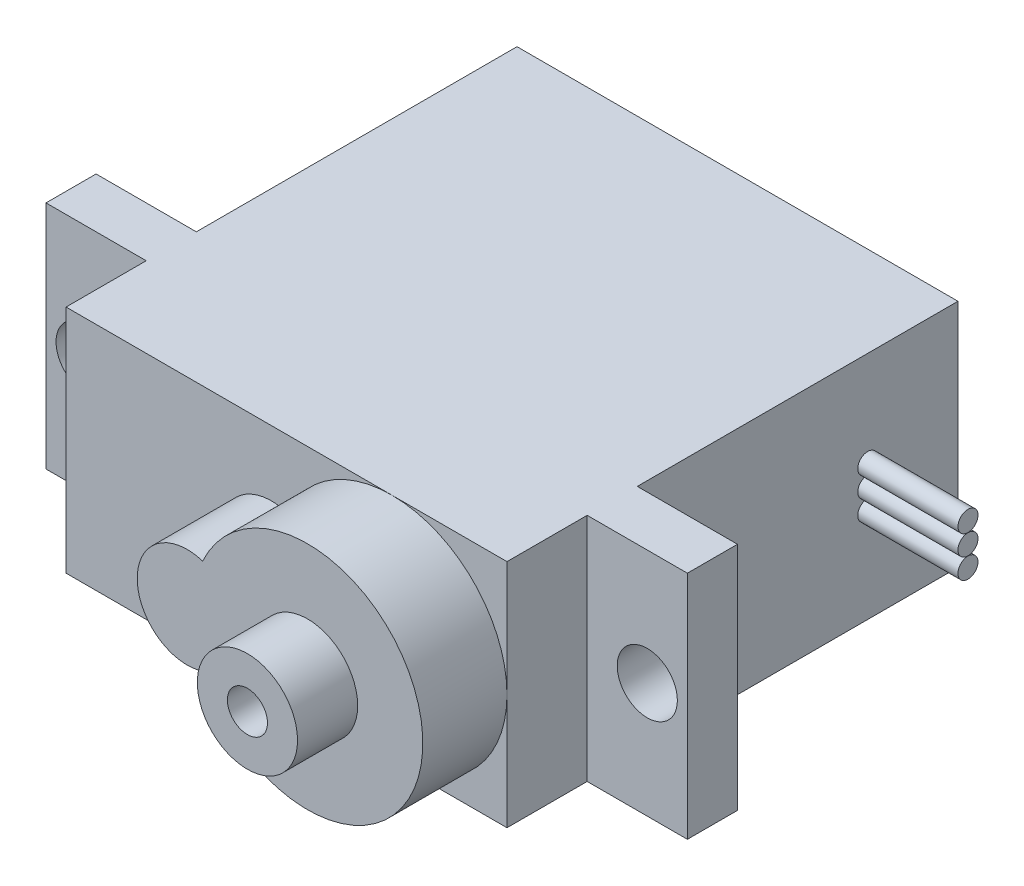
SolidWorks part; units mm, degrees
ref_plane "正面" through (0, 0, 0) normal (0, 0, 1) x (1, 0, 0)
ref_plane "平面" through (0, 0, 0) normal (0, 1, 0) x (1, 0, 0)
ref_plane "右側面" through (0, 0, 0) normal (1, 0, 0) x (0, 0, -1)
sketch "ｽｹｯﾁ1" plane through (0, 0, 0) normal (0, 0, 1) x (1, 0, 0)
  line L1 (0, 0) -> (22, 0)
  line L2 (0, 0) -> (0, 11.5)
  line L3 (0, 11.5) -> (22, 11.5)
  line L4 (22, 0) -> (22, 11.5)
  line L5 (0, 0) -> (22, 11.5) construction
  line L6 (0, 11.5) -> (22, 0) construction
  point P4 (11, 5.75)
  dimension "D1" = 11.5
  dimension "D2" = 22
extrude "ﾎﾞｽ - 押し出し1" add sketch "ｽｹｯﾁ1" along normal blind 16
sketch "ｽｹｯﾁ2" plane through (0, 0, 16) normal (0, 0, 1) x (1, 0, 0)
  line L0 (0, 11.5) -> (22, 11.5) construction
  line L1 (27, 0) -> (-5, 0)
  line L2 (27, 0) -> (27, 11.5)
  line L3 (27, 11.5) -> (-5, 11.5)
  line L4 (-5, 0) -> (-5, 11.5)
  line L5 (27, 0) -> (-5, 11.5) construction
  line L6 (27, 11.5) -> (-5, 0) construction
  point P0 (11, 5.75)
  dimension "D1" = 32
extrude "ﾎﾞｽ - 押し出し2" add sketch "ｽｹｯﾁ2" along normal blind 2.5
sketch "ｽｹｯﾁ3" plane through (0, 0, 18.5) normal (0, 0, 1) x (1, 0, 0)
  line L4 (0, 0) -> (22, 0)
  line L5 (22, 0) -> (22, 11.5)
  line L6 (22, 11.5) -> (0, 11.5)
  line L7 (0, 11.5) -> (0, 0)
  line L8 (0, 0) -> (22, 0)
  line L9 (22, 0) -> (22, 11.5)
  line L10 (22, 11.5) -> (0, 11.5)
  line L11 (0, 11.5) -> (0, 0)
  dimension "D1" = 0
extrude "ﾎﾞｽ - 押し出し3" add sketch "ｽｹｯﾁ3" along normal blind 4
sketch "ｽｹｯﾁ4" plane through (0, 0, 22.5) normal (0, 0, 1) x (1, 0, 0)
  line L1 (10.25, 5.75) -> (16.25, 5.75) construction
  line L2 (0, 11.5) -> (22, 11.5) construction
  line L3 (22, 0) -> (22, 11.5) construction
  line L4 (0, 0) -> (22, 0) construction
  arc A0 (11.0156, 8.1299) -> (11.0156, 3.3701) centre (10.25, 5.75) ccw
  arc A1 (11.0156, 3.3701) -> (11.0156, 8.1299) centre (16.25, 5.75) ccw
  dimension "D1" = 5
  dimension "D2" = 6
extrude "ﾎﾞｽ - 押し出し4" add sketch "ｽｹｯﾁ4" along normal blind 4.2
sketch "ｽｹｯﾁ5" plane through (0, 0, 18.5) normal (0, 0, 1) x (1, 0, 0)
  line L0 (-5, 5.75) -> (27, 5.75) construction
  line L1 (-5, 11.5) -> (-5, 0) construction
  line L2 (27, 0) -> (27, 11.5) construction
  circle A0 centre (-3, 5.75) radius 1.5
  circle A1 centre (25, 5.75) radius 1.5
  dimension "D2" = 3
  dimension "D1" = 28
  dimension "D3" = 14
extrude "ｶｯﾄ - 押し出し1" cut sketch "ｽｹｯﾁ5" against normal through all
sketch "ｽｹｯﾁ6" plane through (22, 0, 0) normal (1, 0, 0) x (0, 0, -1)
  line L0 (-5, 11.5) -> (-5, 0) construction
  line L1 (-16, 11.5) -> (0, 11.5) construction
  line L2 (-16, 0) -> (0, 0) construction
  line L3 (-4.5, 11.5) -> (-4.5, 0) construction
  line L4 (0, 0) -> (0, 11.5) construction
  circle A0 centre (-4.5, 5.75) radius 0.5
  circle A1 centre (-4.5, 6.76) radius 0.5
  circle A3 centre (-4.5, 4.74) radius 0.5
  dimension "D2" = 1
  dimension "D1" = 5
  dimension "D3" = 1.01
  dimension "D4" = 1.01
extrude "ﾎﾞｽ - 押し出し6" add sketch "ｽｹｯﾁ6" along normal blind 5 separate body
sketch "ｽｹｯﾁ7" plane through (0, 0, 26.7) normal (0, 0, 1) x (1, 0, 0)
  circle A0 centre (16.25, 5.75) radius 2.5
  circle A1 centre (16.25, 5.75) radius 1
  dimension "D1" = 2
  dimension "D2" = 5
extrude "ﾎﾞｽ - 押し出し7" add sketch "ｽｹｯﾁ7" along normal blind 3 separate body
sketch "ｽｹｯﾁ8" plane through (0, 0, 0) normal (0, -1, 0) x (1, 0, 0)
  text T0 "SG-90"
extrude "ｶｯﾄ - 押し出し2" cut sketch "ｽｹｯﾁ8" against normal blind 2
equation "\"D3@ｽｹｯﾁ5\"=\"D1@ｽｹｯﾁ5\"/2"
equation "\"D4@ｽｹｯﾁ6\"=\"D3@ｽｹｯﾁ6\""
